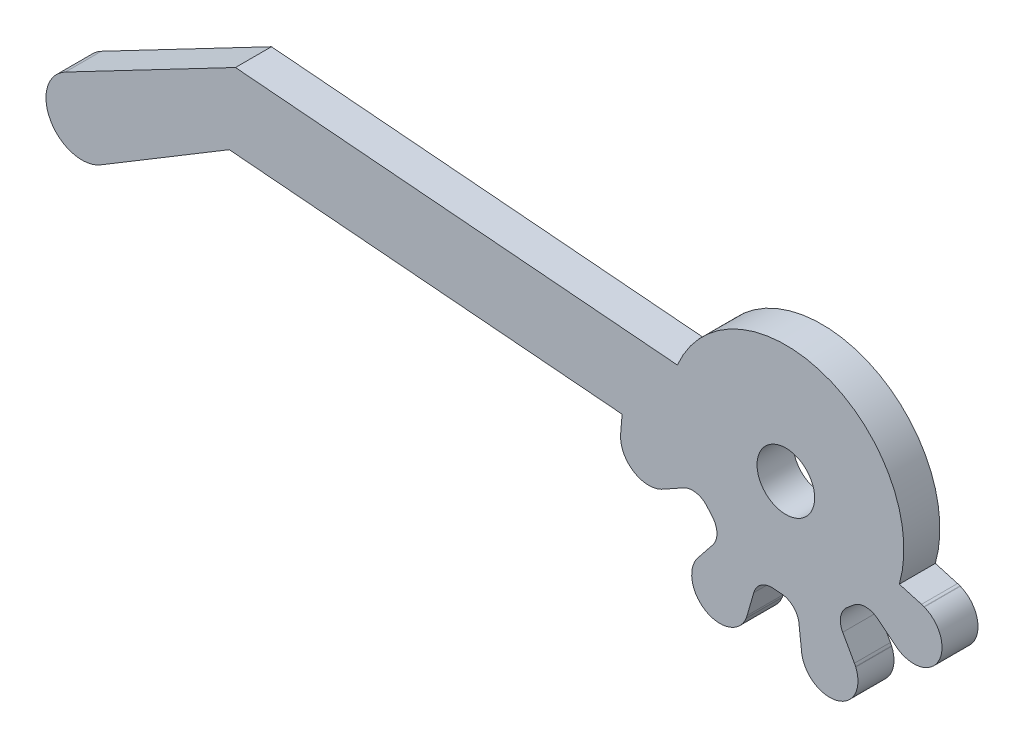
SolidWorks part; units mm, degrees
ref_plane "Alzado" through (0, 0, 0) normal (0, 0, 1) x (1, 0, 0)
ref_plane "Planta" through (0, 0, 0) normal (0, 1, 0) x (1, 0, 0)
ref_plane "Vista lateral" through (0, 0, 0) normal (1, 0, 0) x (0, 0, -1)
sketch "Model" plane through (0, 0, 0) normal (0, 0, 1) x (1, 0, 0)
  line L0 (0.5508, 14.5459) -> (11.2827, 21.007)
  line L1 (11.2827, 21.007) -> (44.0117, 18.2874)
  line L2 (44.0117, 18.2874) -> (43.889, 16.8097)
  line L3 (47.1552, 14.4482) -> (47.1829, 14.4602)
  line L4 (47.3787, 14.5574) -> (49.1274, 15.5297)
  line L5 (51.123, 15.1289) -> (51.5047, 14.678)
  line L6 (51.5706, 12.6436) -> (50.3231, 11.0793)
  line L7 (50.1949, 10.9023) -> (50.1785, 10.877)
  line L8 (54.3463, 8.7305) -> (54.3574, 8.7585)
  line L9 (54.427, 8.9657) -> (54.9761, 10.8897)
  line L10 (56.6706, 12.0174) -> (57.2593, 11.9684)
  line L11 (58.7445, 10.5765) -> (58.9684, 8.5883)
  line L12 (59.003, 8.3724) -> (59.0093, 8.343)
  line L13 (63.4741, 9.7722) -> (63.4622, 9.7998)
  line L14 (63.3649, 9.9956) -> (62.3927, 11.7443)
  line L15 (62.7935, 13.7399) -> (63.2444, 14.1217)
  line L16 (65.2788, 14.1876) -> (66.843, 12.9401)
  line L17 (67.0201, 12.8118) -> (67.0454, 12.7955)
  line L18 (69.1919, 16.9632) -> (69.1639, 16.9743)
  line L19 (68.9567, 17.044) -> (67.1078, 17.5716)
  line L20 (48.6125, 24.1366) -> (11.7969, 27.1957)
  line L21 (11.7969, 27.1957) -> (-2.3785, 19.7795)
  circle A0 centre (57.6527, 20.2697) radius 2.4
  arc A1 (43.889, 16.8097) -> (47.1552, 14.4482) centre (46.2348, 16.6148) ccw
  arc A2 (47.1829, 14.4602) -> (47.3787, 14.5574) centre (46.2348, 16.6148) ccw
  arc A3 (51.123, 15.1289) -> (49.1274, 15.5297) centre (49.89, 14.1581) ccw
  arc A4 (51.5706, 12.6436) -> (51.5047, 14.678) centre (50.3438, 13.6221) ccw
  arc A5 (50.3231, 11.0793) -> (50.1949, 10.9023) centre (52.1634, 9.6116) ccw
  arc A6 (50.1785, 10.877) -> (54.3463, 8.7305) centre (52.1634, 9.6116) ccw
  arc A7 (54.3574, 8.7585) -> (54.427, 8.9657) centre (52.1634, 9.6116) ccw
  arc A8 (56.6706, 12.0174) -> (54.9761, 10.8897) centre (56.4851, 10.4591) ccw
  arc A9 (58.7445, 10.5765) -> (57.2593, 11.9684) centre (57.1851, 10.4009) ccw
  arc A10 (58.9684, 8.5883) -> (59.003, 8.3724) centre (61.3076, 8.8518) ccw
  arc A11 (59.0093, 8.343) -> (63.4741, 9.7722) centre (61.3076, 8.8518) ccw
  arc A12 (63.4622, 9.7998) -> (63.3649, 9.9956) centre (61.3076, 8.8518) ccw
  arc A13 (62.7935, 13.7399) -> (62.3927, 11.7443) centre (63.7643, 12.5069) ccw
  arc A14 (65.2788, 14.1876) -> (63.2444, 14.1217) centre (64.3003, 12.9607) ccw
  arc A15 (66.843, 12.9401) -> (67.0201, 12.8118) centre (68.3108, 14.7804) ccw
  arc A16 (67.0454, 12.7955) -> (69.1919, 16.9632) centre (68.3108, 14.7804) ccw
  arc A17 (69.1639, 16.9743) -> (68.9567, 17.044) centre (68.3108, 14.7804) ccw
  arc A18 (67.1078, 17.5716) -> (48.6125, 24.1366) centre (57.6527, 20.2697) ccw
  arc A19 (-2.3785, 19.7795) -> (0.5508, 14.5459) centre (-0.9878, 17.1213) ccw
  point P51 (0, 0)
extrude "Saliente-Extruir1" add sketch "Model" along normal blind 3
